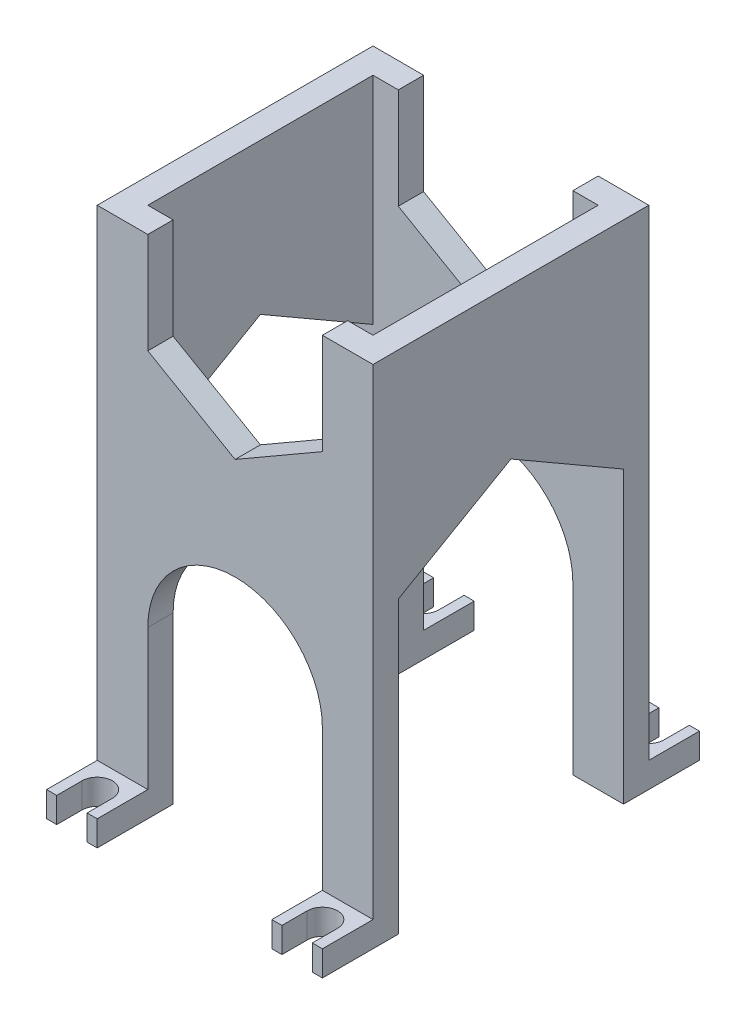
SolidWorks part; units mm, degrees
ref_plane "Plan de face" through (0, 0, 0) normal (0, 0, 1) x (1, 0, 0)
ref_plane "Plan de dessus" through (0, 0, 0) normal (0, 1, 0) x (1, 0, 0)
ref_plane "Plan de droite" through (0, 0, 0) normal (1, 0, 0) x (0, 0, -1)
sketch "Esquisse1" plane through (0, 0, 0) normal (0, 1, 0) x (1, 0, 0)
  line L1 (-21.75, -21.75) -> (21.75, -21.75) construction
  line L2 (-21.75, -21.75) -> (-21.75, 21.75) construction
  line L3 (-21.75, 21.75) -> (21.75, 21.75) construction
  line L4 (21.75, -21.75) -> (21.75, 21.75) construction
  line L5 (-21.75, -21.75) -> (21.75, 21.75) construction
  line L6 (-21.75, 21.75) -> (21.75, -21.75) construction
  line L7 (-22.25, -22.25) -> (22.25, -22.25) construction
  line L8 (-22.25, -22.25) -> (-22.25, 22.25) construction
  line L9 (-22.25, 22.25) -> (22.25, 22.25) construction
  line L10 (22.25, -22.25) -> (22.25, 22.25) construction
  line L11 (-22.25, -22.25) -> (22.25, 22.25) construction
  line L12 (-22.25, 22.25) -> (22.25, -22.25) construction
  line L13 (-27.25, -27.25) -> (27.25, -27.25)
  line L14 (-27.25, -27.25) -> (-27.25, 27.25)
  line L15 (-27.25, 27.25) -> (27.25, 27.25)
  line L16 (27.25, -27.25) -> (27.25, 27.25)
  line L17 (-27.25, -27.25) -> (27.25, 27.25) construction
  line L18 (-27.25, 27.25) -> (27.25, -27.25) construction
  point P0 (0, 0)
  point P6 (0, 0)
  point P11 (0, 0)
  dimension "D1" = 43.5
  dimension "D2" = 0.5
  dimension "D3" = 5
extrude "Boss.-Extru.1" add sketch "Esquisse1" along normal blind 100
sketch "Esquisse2" plane through (27.25, 0, 0) normal (1, 0, 0) x (0, 0, -1)
  line L1 (-22.25, 0) -> (22.25, 0)
  line L2 (-22.25, 0) -> (-22.25, 44.5)
  line L3 (-22.25, 44.5) -> (22.25, 44.5) construction
  line L4 (22.25, 0) -> (22.25, 44.5)
  line L5 (-22.25, 0) -> (22.25, 44.5) construction
  line L6 (-22.25, 44.5) -> (22.25, 0) construction
  line L7 (-27.25, 100) -> (-27.25, 0) construction
  line L16 (-27.25, 0) -> (27.25, 0) construction
  line L17 (-22.25, 57.346) -> (-22.25, 44.5)
  line L18 (0, 70.1921) -> (-22.25, 57.346)
  line L19 (-22.25, 57.346) -> (-22.25, 31.654) construction
  line L20 (-22.25, 31.654) -> (0, 18.8079) construction
  line L21 (0, 18.8079) -> (22.25, 31.654) construction
  line L22 (22.25, 31.654) -> (22.25, 57.346) construction
  line L23 (22.25, 57.346) -> (0, 70.1921)
  line L24 (22.25, 57.346) -> (22.25, 44.5)
  circle A0 centre (0, 44.5) radius 22.25 construction
  point P0 (0, 22.25)
  dimension "D1" = 5
extrude "Enlèv. mat.-Extru.1" cut sketch "Esquisse2" against normal through all
sketch "Esquisse4" plane through (0, 100, 0) normal (0, 1, 0) x (1, 0, 0)
  line L1 (-22.25, -22.25) -> (22.25, -22.25)
  line L2 (-22.25, -22.25) -> (-22.25, 22.25)
  line L3 (-22.25, 22.25) -> (22.25, 22.25)
  line L4 (22.25, -22.25) -> (22.25, 22.25)
  line L5 (-22.25, -22.25) -> (22.25, 22.25) construction
  line L6 (-22.25, 22.25) -> (22.25, -22.25) construction
  point P0 (0, 0)
extrude "Enlèv. mat.-Extru.3" cut sketch "Esquisse4" against normal through all
sketch "Esquisse6" plane through (0, 0, -27.25) normal (0, 0, -1) x (-1, 0, 0)
  line L0 (-27.25, 100) -> (27.25, 100) construction
  line L1 (0, 109.9593) -> (-17.25, 100)
  line L2 (-17.25, 100) -> (-17.25, 80.0814)
  line L3 (-17.25, 80.0814) -> (0, 70.1221)
  line L4 (0, 70.1221) -> (17.25, 80.0814)
  line L5 (17.25, 80.0814) -> (17.25, 100)
  line L6 (17.25, 100) -> (0, 109.9593)
  line L7 (-22.25, 57.346) -> (-22.25, 100) construction
  line L8 (22.25, 57.346) -> (22.25, 100) construction
  line L9 (27.25, 0) -> (-27.25, 0) construction
  line L10 (17.25, 0) -> (-17.25, 0)
  line L11 (17.25, 0) -> (17.25, 32.75)
  line L12 (17.25, 32.75) -> (-17.25, 32.75) construction
  line L13 (-17.25, 0) -> (-17.25, 32.75)
  line L14 (-27.25, 50) -> (27.25, 50) construction
  line L15 (-27.25, 100) -> (-27.25, 0) construction
  line L16 (27.25, 100) -> (27.25, 0) construction
  circle A0 centre (0, 90.0407) radius 17.25 construction
  arc A1 (17.25, 32.75) -> (-17.25, 32.75) centre (0, 32.75) ccw
  point P21 (0, 70.1221)
  dimension "D1" = 5
  dimension "D2" = 5
extrude "Enlèv. mat.-Extru.7" cut sketch "Esquisse6" against normal through all
sketch "Esquisse11" plane through (0, 0, 0) normal (0, 1, 0) x (1, 0, 0)
  line L0 (0, 27.25) -> (0, -27.25) construction
  line L1 (19.25, 37.25) -> (19.25, 32.25)
  line L2 (25.25, 37.25) -> (25.25, 32.25)
  line L3 (-27.25, 27.25) -> (27.25, 27.25) construction
  line L4 (25.25, 37.25) -> (27.25, 37.25)
  line L5 (27.25, 22.25) -> (27.25, 37.25)
  line L7 (-27.25, -27.25) -> (27.25, -27.25) construction
  line L8 (-27.25, 0) -> (27.25, 0) construction
  line L16 (-27.25, -27.25) -> (-27.25, 27.25) construction
  line L17 (27.25, -27.25) -> (27.25, 27.25) construction
  line L19 (-17.25, 22.25) -> (-27.25, 22.25)
  line L20 (-17.25, 22.25) -> (-17.25, 37.25)
  line L21 (-17.25, 37.25) -> (-19.25, 37.25)
  line L22 (-27.25, 22.25) -> (-27.25, 37.25)
  line L23 (-25.25, 37.25) -> (-27.25, 37.25)
  line L25 (-25.25, 37.25) -> (-25.25, 32.25)
  line L27 (-19.25, 37.25) -> (-19.25, 32.25)
  line L28 (17.25, 37.25) -> (19.25, 37.25)
  line L29 (17.25, 22.25) -> (17.25, 37.25)
  line L30 (17.25, 22.25) -> (27.25, 22.25)
  line L31 (17.25, -22.25) -> (27.25, -22.25)
  line L32 (17.25, -22.25) -> (17.25, -37.25)
  line L33 (17.25, -37.25) -> (19.25, -37.25)
  line L34 (-19.25, -37.25) -> (-19.25, -32.25)
  line L35 (-25.25, -37.25) -> (-25.25, -32.25)
  line L36 (-25.25, -37.25) -> (-27.25, -37.25)
  line L37 (-27.25, -22.25) -> (-27.25, -37.25)
  line L38 (-17.25, -37.25) -> (-19.25, -37.25)
  line L39 (-17.25, -22.25) -> (-17.25, -37.25)
  line L40 (-17.25, -22.25) -> (-27.25, -22.25)
  line L41 (27.25, -22.25) -> (27.25, -37.25)
  line L42 (25.25, -37.25) -> (27.25, -37.25)
  line L43 (25.25, -37.25) -> (25.25, -32.25)
  line L44 (19.25, -37.25) -> (19.25, -32.25)
  arc A11 (-25.25, 32.25) -> (-19.25, 32.25) centre (-22.25, 32.25) ccw
  arc A12 (25.25, 32.25) -> (19.25, 32.25) centre (22.25, 32.25) cw
  arc A13 (25.25, -32.25) -> (19.25, -32.25) centre (22.25, -32.25) ccw
  arc A14 (-25.25, -32.25) -> (-19.25, -32.25) centre (-22.25, -32.25) cw
  point P4 (-24.5488, 32.303)
  point P5 (-32.0705, 17.25)
  point P14 (-21.75, 20.7374)
  point P19 (0, 0)
  point P26 (0, 0)
  point P29 (0, 0)
  dimension "D1" = 15
  dimension "D3" = 3
  dimension "D2" = 5
extrude "Boss.-Extru.2" add sketch "Esquisse11" along normal blind 5
